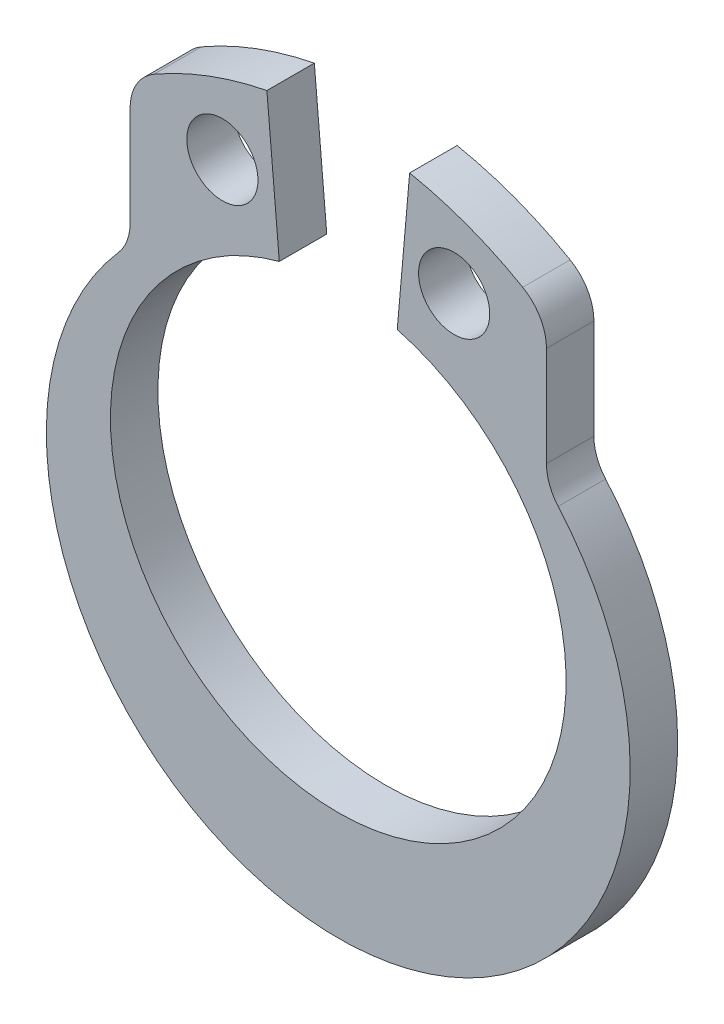
SolidWorks part; units mm, degrees
material "AISI 4130 Steel, annealed at 865C"
ref_plane "Plane1" through (0, 0, 0) normal (0, 0, 1) x (1, 0, 0)
ref_plane "Plane2" through (0, 0, 0) normal (0, 1, 0) x (-1, 0, 0)
ref_plane "Plane3" through (0, 0, 0) normal (1, 0, 0) x (0, 0, -1)
sketch "Sketch1" plane through (0, 0, 0) normal (0, 0, 1) x (1, 0, 0)
  line L0 (0, 0.9398) -> (1.2423, 5.5762) construction
  line L1 (0, 0.9398) -> (-1.2423, 5.5762) construction
  line L2 (-4.386, 6.8044) -> (-4.386, 4.7026)
  line L3 (4.386, 4.7026) -> (4.386, 6.8044)
  line L4 (-1.2423, 5.5762) -> (-1.5038, 8.5648)
  line L5 (1.2423, 5.5762) -> (1.5038, 8.5648)
  line L6 (0, 0.9398) -> (3.386, 6.8044) construction
  line L7 (0, 0.9398) -> (-3.386, 6.8044) construction
  line L8 (2.4415, 6.8342) -> (0, 0.9398) construction
  line L9 (-2.4415, 6.8342) -> (0, 0.9398) construction
  arc A0 (-4.6327, 4.0449) -> (4.6327, 4.0449) centre (0, 0) ccw
  arc A1 (-1.2423, 5.5762) -> (1.2423, 5.5762) centre (0, 0.9398) ccw
  arc A2 (-3.886, 7.6705) -> (-1.5038, 8.5648) centre (0, 0.9398) cw
  arc A3 (1.5038, 8.5648) -> (3.886, 7.6705) centre (0, 0.9398) cw
  arc A4 (-4.386, 4.7026) -> (-4.6327, 4.0449) centre (-5.386, 4.7026) cw
  arc A5 (-3.886, 7.6705) -> (-4.386, 6.8044) centre (-3.386, 6.8044) ccw
  arc A6 (4.6327, 4.0449) -> (4.386, 4.7026) centre (5.386, 4.7026) cw
  arc A7 (4.386, 6.8044) -> (3.886, 7.6705) centre (3.386, 6.8044) ccw
  circle A8 centre (-2.4415, 6.8342) radius 0.75
  circle A9 centre (2.4415, 6.8342) radius 0.75
  dimension "D1" = 9.6
  dimension "D2" = 12.3
  dimension "D7" = 3
  dimension "D8" = 1
  dimension "D9" = 1.5
  dimension "D10" = 6.38
  dimension "D3" = 0.9398
  dimension "D4" = 30
  dimension "D5" = 60
  dimension "D6" = 10
  dimension "D11" = 45
extrude "Base-Extrude" add sketch "Sketch1" along normal blind 1
